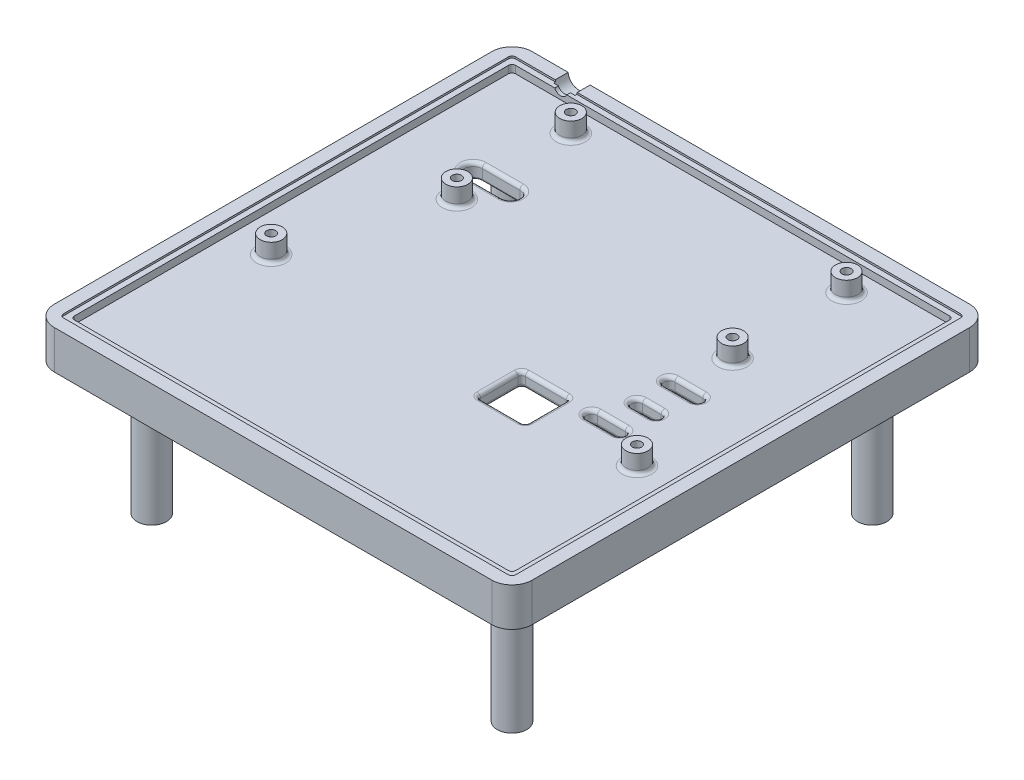
SolidWorks part; units mm, degrees
ref_plane "Front" through (0, 0, 0) normal (0, 0, 1) x (1, 0, 0)
ref_plane "Top" through (0, 0, 0) normal (0, 1, 0) x (1, 0, 0)
ref_plane "Right" through (0, 0, 0) normal (1, 0, 0) x (0, 0, -1)
sketch "Sketch1" plane through (0, 0, 0) normal (0, 1, 0) x (1, 0, 0)
  line L0 (-65, 59.5) -> (-65, -59.5)
  line L1 (-59.5, -65) -> (59.5, -65)
  line L2 (65, -59.5) -> (65, 59.5)
  line L7 (59.5, 65) -> (-59.5, 65)
  arc A0 (-59.5, 65) -> (-65, 59.5) centre (-59.5, 59.5) ccw
  arc A1 (-59.5, -65) -> (-65, -59.5) centre (-59.5, -59.5) cw
  arc A3 (65, -59.5) -> (59.5, -65) centre (59.5, -59.5) cw
  arc A4 (65, 59.5) -> (59.5, 65) centre (59.5, 59.5) ccw
extrude "Boss-Extrude1" add sketch "Sketch1" along normal blind 10
sketch "Sketch2" plane through (0, 0, 0) normal (0, -1, 0) x (1, 0, 0)
  line L3 (-60, -60) -> (60, -60)
  line L4 (-60, -60) -> (-60, 60)
  line L5 (-60, 60) -> (60, 60)
  line L6 (60, -60) -> (60, 60)
extrude "Cut-Extrude1" cut sketch "Sketch2" against normal blind 4
fillet "Fillet1" radius 1 4 edges at (60, 2, 60) (60, 2, -60) (-60, 2, 60) (-60, 2, -60)
sketch "Sketch3" plane through (0, 10, 0) normal (0, 1, 0) x (1, 0, 0)
  line L3 (-60, -60) -> (60, -60)
  line L4 (-60, -60) -> (-60, 60)
  line L5 (-60, 60) -> (60, 60)
  line L6 (60, -60) -> (60, 60)
extrude "Cut-Extrude2" cut sketch "Sketch3" against normal blind 2
fillet "Fillet2" radius 1 4 edges at (60, 9, 60) (60, 9, -60) (-60, 9, -60) (-60, 9, 60)
sketch "Sketch4" plane through (0, 10, 0) normal (0, 1, 0) x (1, 0, 0)
  line L2 (-59.5, -65) -> (59.5, -65)
  line L3 (-61.5, -61.5) -> (61.5, -61.5)
  line L4 (-61.5, -61.5) -> (-61.5, 61.5)
  line L5 (-61.5, 61.5) -> (61.5, 61.5)
  line L6 (61.5, -61.5) -> (61.5, 61.5)
  line L7 (-65, -59.5) -> (-65, 59.5)
  line L14 (-59.5, 65) -> (59.5, 65)
  line L15 (65, 59.5) -> (65, -59.5)
  arc A0 (-59.5, 65) -> (-65, 59.5) centre (-59.5, 59.5) ccw
  arc A1 (-59.5, 65) -> (-65, 59.5) centre (-59.5, 59.5) ccw construction
  arc A2 (59.5, 65) -> (65, 59.5) centre (59.5, 59.5) cw
  arc A3 (65, -59.5) -> (59.5, -65) centre (59.5, -59.5) cw
  arc A4 (-65, -59.5) -> (-59.5, -65) centre (-59.5, -59.5) ccw
extrude "Boss-Extrude2" add sketch "Sketch4" along normal blind 0.5
fillet "Fillet3" radius 1 1 edges at (61.5, 10.25, -61.5)
fillet "Fillet4" radius 1 1 edges at (-61.5, 10.25, -61.5)
fillet "Fillet5" radius 1 1 edges at (-61.5, 10.25, 61.5)
fillet "Fillet6" radius 1 1 edges at (61.5, 10.25, 61.5)
sketch "Sketch9" plane through (0, 0, -65) normal (0, 0, -1) x (-1, 0, 0)
  line L0 (44.9689, 10.5) -> (48.5311, 10.5)
  arc A1 (48.5311, 10.5) -> (44.9689, 10.5) centre (46.75, 10.76) cw
extrude "Cut-Extrude8" cut sketch "Sketch9" against normal blind 5
sketch "Sketch11" plane through (0, 0, -65) normal (0, 0, -1) x (-1, 0, 0)
  line L0 (43.7613, 10.5) -> (49.7387, 10.5)
  arc A1 (49.7387, 10.5) -> (43.7613, 10.5) centre (46.75, 10.76) cw
extrude "Cut-Extrude9" cut sketch "Sketch11" against normal blind 4
sketch "Sketch12" plane through (0, 8, 0) normal (0, 1, 0) x (1, 0, 0)
  circle A0 centre (-37.5, 53.5) radius 3
extrude "Boss-Extrude4" add sketch "Sketch12" along normal blind 5
sketch "Sketch14" plane through (0, 8, 0) normal (0, 1, 0) x (1, 0, 0)
  circle A0 centre (37.5, 53.5) radius 3
extrude "Boss-Extrude5" add sketch "Sketch14" along normal blind 5
sketch "Sketch15" plane through (0, 8, 0) normal (0, 1, 0) x (1, 0, 0)
  circle A0 centre (-37.5, 22.5) radius 3
  circle A1 centre (37.5, 22.5) radius 3
extrude "Boss-Extrude6" add sketch "Sketch15" along normal blind 5
sketch "Sketch16" plane through (0, 13, 0) normal (0, 1, 0) x (1, 0, 0)
  circle A0 centre (-37.5, 53.5) radius 1.25
extrude "Cut-Extrude11" cut sketch "Sketch16" against normal blind 9
sketch "Sketch17" plane through (0, 13, 0) normal (0, 1, 0) x (1, 0, 0)
  circle A0 centre (37.5, 53.5) radius 1.25
extrude "Cut-Extrude12" cut sketch "Sketch17" against normal blind 9
sketch "Sketch18" plane through (0, 13, 0) normal (0, 1, 0) x (1, 0, 0)
  circle A0 centre (-37.5, 22.5) radius 1.25
extrude "Cut-Extrude13" cut sketch "Sketch18" against normal blind 9
sketch "Sketch20" plane through (0, 13, 0) normal (0, 1, 0) x (1, 0, 0)
  circle A0 centre (37.5, 22.5) radius 1.25
extrude "Cut-Extrude14" cut sketch "Sketch20" against normal blind 9
sketch "Sketch21" plane through (0, 4, 0) normal (0, -1, 0) x (1, 0, 0)
  circle A0 centre (37.5, -22.5) radius 3
  circle A1 centre (37.5, -53.5) radius 3
  circle A2 centre (-37.5, -22.5) radius 3
  circle A3 centre (-37.5, -53.5) radius 3
extrude "Cut-Extrude15" cut sketch "Sketch21" against normal blind 1
sketch "Sketch24" plane through (0, 8, 0) normal (0, 1, 0) x (1, 0, 0)
  circle A0 centre (-49.7, -15.8) radius 3
  circle A1 centre (49.8, -15.8) radius 3
extrude "Boss-Extrude8" add sketch "Sketch24" along normal blind 5
sketch "Sketch25" plane through (0, 13, 0) normal (0, 1, 0) x (1, 0, 0)
  circle A0 centre (-49.7, -15.8) radius 1.25
  circle A1 centre (49.8, -15.8) radius 1.25
extrude "Cut-Extrude17" cut sketch "Sketch25" against normal blind 9
sketch "Sketch26" plane through (0, 4, 0) normal (0, -1, 0) x (1, 0, 0)
  circle A0 centre (49.8, 15.8) radius 3
  circle A1 centre (-49.7, 15.8) radius 3
extrude "Cut-Extrude18" cut sketch "Sketch26" against normal blind 1
sketch "Sketch27" plane through (0, 8, 0) normal (0, 1, 0) x (1, 0, 0)
  line L6 (-32, 31.6135) -> (-42.18, 31.6135) construction
  line L7 (-32, 29.1135) -> (-42.18, 29.1135)
  line L10 (-32, 34.1135) -> (-42.18, 34.1135)
  arc A2 (-32, 29.1135) -> (-32, 34.1135) centre (-32, 31.6135) ccw
  arc A3 (-42.18, 34.1135) -> (-42.18, 29.1135) centre (-42.18, 31.6135) ccw
  point P5 (-37.09, 31.6135)
sketch "Sketch28" plane through (0, 4, 0) normal (0, -1, 0) x (1, 0, 0)
  line L0 (39.22, 9.8842) -> (31.6, 9.8842) construction
  line L2 (39.22, 8.3842) -> (31.6, 8.3842)
  line L3 (39.22, 11.3842) -> (31.6, 11.3842)
  arc A0 (39.22, 8.3842) -> (39.22, 11.3842) centre (39.22, 9.8842) ccw
  arc A1 (31.6, 11.3842) -> (31.6, 8.3842) centre (31.6, 9.8842) ccw
  point P3 (35.41, 9.8842)
extrude "Cut-Extrude20" cut sketch "Sketch28" against normal blind 4
fillet "Fillet9" radius 1 4 edges at (30.1, 4, 9.8842) (35.41, 4, 11.3842) (40.72, 4, 9.8842) (35.41, 4, 8.3842)
fillet "Fillet10" radius 1 4 edges at (30.1, 8, 9.8842) (35.41, 8, 8.3842) (35.41, 8, 11.3842) (40.72, 8, 9.8842)
sketch "Sketch29" plane through (0, 4, 0) normal (0, -1, 0) x (1, 0, 0)
  line L0 (41.9, -8.5085) -> (34.28, -8.5085) construction
  line L2 (41.9, -10.0085) -> (34.28, -10.0085)
  line L5 (41.9, -7.0085) -> (34.28, -7.0085)
  arc A0 (41.9, -10.0085) -> (41.9, -7.0085) centre (41.9, -8.5085) ccw
  arc A1 (34.28, -7.0085) -> (34.28, -10.0085) centre (34.28, -8.5085) ccw
  point P3 (38.09, -8.5085)
extrude "Cut-Extrude21" cut sketch "Sketch29" against normal blind 4
fillet "Fillet11" radius 1 8 edges at (38.09, 8, -10.0085) (38.09, 4, -10.0085) (32.78, 8, -8.5085) (32.78, 4, -8.5085) (43.4, 8, -8.5085) (43.4, 4, -8.5085) (38.09, 8, -7.0085) (38.09, 4, -7.0085)
sketch "Sketch30" plane through (0, 4, 0) normal (0, -1, 0) x (1, 0, 0)
  line L0 (40.09, 0.9966) -> (35.01, 0.9966) construction
  line L2 (40.09, -0.5034) -> (35.01, -0.5034)
  line L5 (40.09, 2.4966) -> (35.01, 2.4966)
  arc A0 (40.09, -0.5034) -> (40.09, 2.4966) centre (40.09, 0.9966) ccw
  arc A1 (35.01, 2.4966) -> (35.01, -0.5034) centre (35.01, 0.9966) ccw
  point P3 (37.55, 0.9966)
extrude "Cut-Extrude22" cut sketch "Sketch30" against normal blind 4
fillet "Fillet12" radius 1 8 edges at (37.55, 8, 2.4966) (37.55, 4, 2.4966) (41.59, 8, 0.9966) (41.59, 4, 0.9966) (37.55, 8, -0.5034) (37.55, 4, -0.5034) (33.51, 8, 0.9966) (33.51, 4, 0.9966)
sketch "Sketch31" plane through (0, 4, 0) normal (0, -1, 0) x (1, 0, 0)
  line L3 (23.71, 8.99) -> (12.63, 8.99)
  line L4 (11.63, 9.99) -> (11.63, 20.15)
  line L15 (12.63, 21.15) -> (23.71, 21.15)
  line L16 (24.71, 20.15) -> (24.71, 9.99)
  arc A0 (24.71, 9.99) -> (23.71, 8.99) centre (23.71, 9.99) cw
  arc A1 (24.71, 20.15) -> (23.71, 21.15) centre (23.71, 20.15) ccw
  arc A2 (12.63, 21.15) -> (11.63, 20.15) centre (12.63, 20.15) ccw
  arc A3 (12.63, 8.99) -> (11.63, 9.99) centre (12.63, 9.99) cw
extrude "Cut-Extrude23" cut sketch "Sketch31" against normal blind 4
fillet "Fillet13" radius 1 16 edges at (24.4171, 8, 20.8571) (24.4171, 4, 20.8571) (18.17, 8, 21.15) (18.17, 4, 21.15) (11.9229, 8, 20.8571) (11.9229, 4, 20.8571) (11.63, 8, 15.07) (11.63, 4, 15.07) (11.9229, 8, 9.2829) (11.9229, 4, 9.2829) (18.17, 8, 8.99) (18.17, 4, 8.99) (24.4171, 8, 9.2829) (24.4171, 4, 9.2829) (24.71, 8, 15.07) (24.71, 4, 15.07)
sketch "Sketch32" plane through (0, 4, 0) normal (0, -1, 0) x (1, 0, 0)
  text T0 "BATTERY" font "Century Gothic" height 2
extrude "Cut-Extrude24" cut sketch "Sketch32" against normal blind 0.2
sketch "Sketch33" plane through (0, 4, 0) normal (0, -1, 0) x (1, 0, 0)
  text T0 "PROG/DEBUG" font "Century Gothic" height 2
extrude "Cut-Extrude25" cut sketch "Sketch33" against normal blind 0.2
sketch "Sketch34" plane through (0, 4, 0) normal (0, -1, 0) x (1, 0, 0)
  text T0 "LOCK S" font "Century Gothic" height 2
extrude "Cut-Extrude26" cut sketch "Sketch34" against normal blind 0.2
sketch "Sketch35" plane through (0, 4, 0) normal (0, -1, 0) x (1, 0, 0)
  text T0 "UNLOCK S" font "Century Gothic" height 2
extrude "Cut-Extrude27" cut sketch "Sketch35" against normal blind 0.2
sketch "Sketch37" plane through (0, 4, 0) normal (0, -1, 0) x (1, 0, 0)
  text T0 "MOTOR" font "Century Gothic" height 2
sketch "Sketch39" plane through (0, 4, 0) normal (0, -1, 0) x (1, 0, 0)
  circle A0 centre (49, -49) radius 4
  circle A1 centre (-49, -49) radius 4
  circle A2 centre (49, 49) radius 4
  circle A3 centre (-49, 49) radius 4
extrude "Cut-Extrude29" cut sketch "Sketch37" against normal blind 0.2
extrude "Boss-Extrude9" add sketch "Sketch39" along normal blind 40
sketch "Sketch40" plane through (0, -36, 0) normal (0, -1, 0) x (-1, 0, 0)
  circle A0 centre (-49, 49) radius 1.2
  circle A1 centre (49, 49) radius 1.2
  circle A2 centre (49, -49) radius 1.2
  circle A3 centre (-49, -49) radius 1.2
extrude "Cut-Extrude30" cut sketch "Sketch40" against normal blind 20
extrude "Cut-Extrude31" cut sketch "Sketch27" against normal blind 4
fillet "Fillet14" radius 0.5 4 edges at (-44.68, 4, -31.6135) (-37.09, 4, -34.1135) (-29.5, 4, -31.6135) (-37.09, 4, -29.1135)
fillet "Fillet15" radius 1 4 edges at (-29.5, 8, -31.6135) (-37.09, 8, -29.1135) (-44.68, 8, -31.6135) (-37.09, 8, -34.1135)
sketch "Sketch41" plane through (0, 4, 0) normal (0, -1, 0) x (1, 0, 0)
  circle A0 centre (-36, -39) radius 1.025
  circle A1 centre (-11.1, -39) radius 1.025
  circle A2 centre (-11.1, 25.9) radius 1.025
  circle A3 centre (-36, 25.9) radius 1.025
extrude "Cut-Extrude32" cut sketch "Sketch41" against normal blind 3
fillet "Fillet16" radius 1 4 edges at (49, 4, -45) (-49, 4, -45) (-49, 4, 53) (49, 4, 53)
fillet "Fillet17" radius 1 6 edges at (-37.5, 8, -56.5) (37.5, 8, -56.5) (37.5, 8, -25.5) (49.8, 8, 12.8) (-49.7, 8, 12.8) (-37.5, 8, -25.5)
